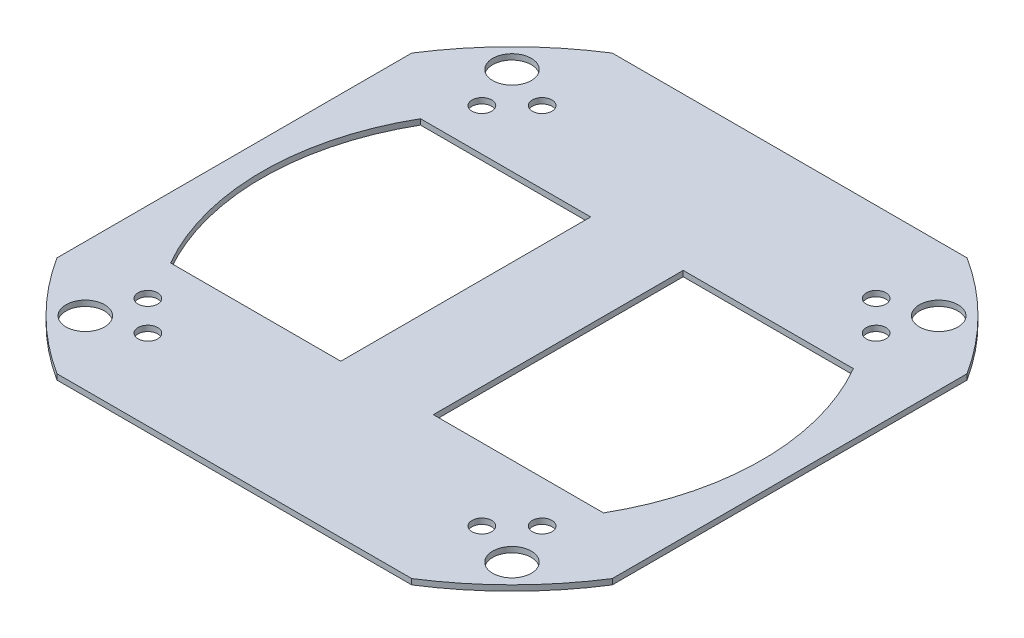
SolidWorks part; units mm, degrees
material "Hexcel AS4C (3000 丝)"
ref_plane "Front" through (0, 0, 0) normal (0, 0, 1) x (1, 0, 0)
ref_plane "Top" through (0, 0, 0) normal (0, 1, 0) x (1, 0, 0)
ref_plane "Right" through (0, 0, 0) normal (1, 0, 0) x (0, 0, -1)
sketch "草图3" plane through (0, 0, 0) normal (0, 1, 0) x (1, 0, 0)
  line L0 (0, 0) -> (125.865, 125.865) construction
  line L1 (0, 0) -> (-125.865, -125.865) construction
  line L2 (0, 0) -> (-125.865, 125.865) construction
  line L3 (0, 0) -> (125.865, -125.865) construction
  line L4 (0, 67.5) -> (0, 0) construction
  line L5 (0, 0) -> (0, 33.75) construction
  line L6 (0, 33.75) -> (25, 33.75) construction
  line L7 (0, 33.75) -> (-25, 33.75) construction
  line L8 (-25, 33.75) -> (-25, -67.5)
  line L9 (-25, 33.75) -> (-25, 67.5)
  line L10 (25, 33.75) -> (25, 67.5)
  line L11 (25, 33.75) -> (25, -67.5)
  line L27 (-135, 0) -> (0, 0) construction
  line L28 (0, 0) -> (-67.5, 0) construction
  line L29 (-67.5, 0) -> (0, 0) construction
  line L30 (0, 0) -> (135, 0) construction
  line L31 (135, 0) -> (67.5, 0) construction
  line L32 (0, -135) -> (0, 0) construction
  line L33 (0, 0) -> (0, 135) construction
  line L34 (0, 135) -> (0, 67.5) construction
  line L35 (0, 67.5) -> (0, 0) construction
  line L36 (0, 0) -> (0, -67.5) construction
  line L37 (0, -67.5) -> (0, -135) construction
  line L38 (25, 67.5) -> (116.9134, 67.5)
  line L39 (-25, 67.5) -> (-116.9134, 67.5)
  line L40 (25, -67.5) -> (116.9134, -67.5)
  line L41 (-25, -67.5) -> (-116.9134, -67.5)
  arc A0 (-116.9134, 67.5) -> (-116.9134, -67.5) centre (0, 0) ccw
  arc A5 (116.9134, -67.5) -> (116.9134, 67.5) centre (0, 0) ccw
  circle A6 centre (0, 0) radius 178
  point P36 (0, 0)
extrude "凸台-拉伸3" add sketch "草图3" along normal blind 3
sketch "草图4" plane through (0, 3, 0) normal (0, 1, 0) x (1, 0, 0)
  line L0 (-115.2584, -115.2584) -> (-125.865, -125.865) construction
  line L1 (125.865, 125.865) -> (115.2584, 115.2584) construction
  line L2 (-125.865, -125.865) -> (-95.8738, -95.8738) construction
  line L3 (-95.8738, -95.8738) -> (-90.2169, -101.5306) construction
  line L4 (-90.2169, -101.5306) -> (-95.1667, -106.4804) construction
  line L5 (-95.1667, -106.4804) -> (-90.2169, -111.4301) construction
  line L6 (-90.2169, -111.4301) -> (-90.2169, -101.5306) construction
  line L7 (-90.2169, -101.5306) -> (-90.2169, -106.4804) construction
  line L8 (-90.2169, -106.4804) -> (-95.1667, -106.4804) construction
  line L9 (-125.865, 125.865) -> (-95.8738, 95.8738) construction
  line L10 (125.865, 125.865) -> (95.8738, 95.8738) construction
  line L11 (125.865, -125.865) -> (95.8738, -95.8738) construction
  circle A0 centre (0, 0) radius 178 construction
  circle A1 centre (115.2584, 115.2584) radius 10.414
  circle A2 centre (115.2584, -115.2584) radius 10.414
  circle A3 centre (-115.2584, -115.2584) radius 10.414
  circle A4 centre (-115.2584, 115.2584) radius 10.414
  circle A5 centre (-90.2169, -106.4804) radius 5.3
  circle A6 centre (-106.4804, -90.2169) radius 5.3
  circle A7 centre (-106.4804, 90.2169) radius 5.3
  circle A8 centre (-90.2169, 106.4804) radius 5.3
  circle A9 centre (90.2169, 106.4804) radius 5.3
  circle A10 centre (106.4804, 90.2169) radius 5.3
  circle A11 centre (106.4804, -90.2169) radius 5.3
  circle A12 centre (90.2169, -106.4804) radius 5.3
  point P16 (0, 0)
  point P43 (0, 0)
  dimension "D1" = 4
extrude "切除-拉伸1" cut sketch "草图4" against normal blind 10
sketch "草图5" plane through (0, 3, 0) normal (0, 1, 0) x (1, 0, 0)
  line L0 (0, 0) -> (150, 0) construction
  line L1 (150, 0) -> (150, 95.8332) construction
  line L2 (0, 0) -> (0, 150) construction
  line L3 (0, 150) -> (95.8332, 150) construction
  line L4 (95.8332, 150) -> (0, 150)
  line L5 (0, 150) -> (-95.8332, 150)
  line L6 (150, 95.8332) -> (150, 0)
  line L7 (150, 0) -> (150, -95.8332)
  line L8 (95.8332, -150) -> (0, -150)
  line L9 (0, -150) -> (-95.8332, -150)
  line L10 (-150, 0) -> (-150, -95.8332)
  line L11 (-150, 95.8332) -> (-150, 0)
  circle A0 centre (0, 0) radius 178 construction
  arc A1 (-150, 95.8332) -> (-150, -95.8332) centre (0, 0) ccw
  arc A2 (150, -95.8332) -> (150, 95.8332) centre (0, 0) ccw
  arc A3 (-95.8332, -150) -> (95.8332, -150) centre (0, 0) ccw
  arc A4 (95.8332, 150) -> (-95.8332, 150) centre (0, 0) ccw
extrude "切除-拉伸2" cut sketch "草图5" against normal blind 10
